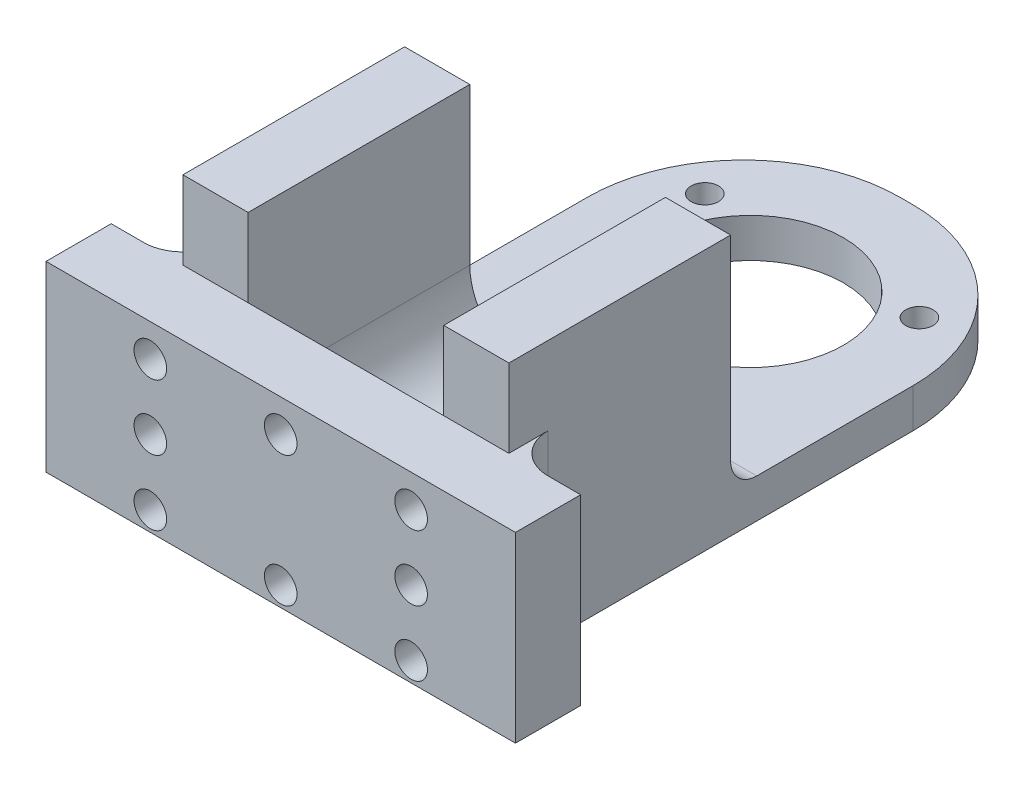
SolidWorks part; units mm, degrees
ref_plane "Front Plane" through (0, 0, 0) normal (0, 0, 1) x (1, 0, 0)
ref_plane "Top Plane" through (0, 0, 0) normal (0, 1, 0) x (1, 0, 0)
ref_plane "Right Plane" through (0, 0, 0) normal (1, 0, 0) x (0, 0, -1)
sketch "Sketch1" plane through (0, 0, 0) normal (0, 0, 1) x (1, 0, 0)
  line L1 (-12.5, -10) -> (12.5, -10)
  line L2 (-12.5, -10) -> (-12.5, 10)
  line L3 (-12.5, 10) -> (12.5, 10)
  line L4 (12.5, -10) -> (12.5, 10)
  line L5 (-12.5, -10) -> (12.5, 10) construction
  line L6 (-12.5, 10) -> (12.5, -10) construction
  point P0 (0, 0)
  point P11 (0, 0)
  point P13 (0, 0.5)
  dimension "D1" = 25
  dimension "D2" = 20
extrude "Main" add sketch "Sketch1" along normal blind 43
sketch "Sketch5" plane through (0, -10, 0) normal (0, -1, 0) x (-1, 0, 0)
  line L0 (0, -21.5) -> (-8.2272, -7.25) construction
  line L1 (-8.2272, -7.25) -> (8.2272, -7.25) construction
  line L2 (8.2272, -7.25) -> (0, -21.5) construction
  line L4 (12.5, 0) -> (-12.5, 0) construction
  circle A0 centre (0, -12) radius 9.5 construction
  circle A1 centre (0, -21.5) radius 1.05
  circle A2 centre (-8.2272, -7.25) radius 1.05
  circle A3 centre (8.2272, -7.25) radius 1.05
  circle A4 centre (0, -12) radius 7.15
  point P11 (0, 0)
  point P12 (0, -12.5)
  point P13 (0, 0)
  point P14 (0, -12.5)
  point P16 (-9.4545, -9.7951)
  point P17 (0, 0)
  point P18 (0, 0)
  dimension "D1" = 19
  dimension "D2" = 2.1
  dimension "D4" = 14.3
  dimension "D3" = 12
extrude "MainAndFixHole" cut sketch "Sketch5" against normal through all
sketch "Sketch6" plane through (0, -10, 0) normal (0, -1, 0) x (-1, 0, 0)
  circle A0 centre (0, -21.5) radius 2.2
  circle A1 centre (-8.2272, -7.25) radius 2.2
  circle A2 centre (8.2272, -7.25) radius 2.2
  dimension "D1" = 4.4
extrude "CoderFixHole2" cut sketch "Sketch6" against normal blind 1.5
sketch "Sketch7" plane through (12.5, 0, 0) normal (1, 0, 0) x (0, 0, -1)
  line L1 (-26, 10) -> (0, 10)
  line L2 (-26, 10) -> (-26, -7)
  line L3 (-26, -7) -> (0, -7)
  line L4 (0, 10) -> (0, -7)
  line L5 (-43, -10) -> (0, -10) construction
  line L7 (0, -10) -> (0, 10) construction
  point P4 (0, 10)
  point P6 (0, 10)
  point P9 (0, -7)
  dimension "D1" = 3
  dimension "D2" = 26
extrude "CoderHole" cut sketch "Sketch7" against normal through all
sketch "Sketch10" plane through (0, 0, 43) normal (0, 0, 1) x (1, 0, 0)
  line L0 (-12.5, -10) -> (12.5, -10) construction
  line L1 (-18, -10) -> (18, -10)
  line L2 (-18, -10) -> (-18, 4)
  line L3 (-18, 4) -> (18, 4)
  line L4 (18, -10) -> (18, 4)
  point P4 (0, -10)
  point P5 (0, -10)
  point P6 (0, 0)
  point P9 (0, -12.7416)
  dimension "D1" = 14
  dimension "D2" = 36
  dimension "D3" = 0
extrude "Link" add sketch "Sketch10" along normal blind 5
sketch "Sketch8" plane through (0, 0, 48) normal (0, 0, 1) x (1, 0, 0)
  line L0 (-10, 1.5) -> (10, 1.5) construction
  line L1 (12.5, 10) -> (-12.5, 10) construction
  line L4 (-18, -10) -> (18, -10) construction
  circle A0 centre (-10, 1.5) radius 1.25
  circle A1 centre (-10, -8.5) radius 1.25
  circle A2 centre (10, -8.5) radius 1.25
  circle A3 centre (10, 1.5) radius 1.25
  circle A4 centre (-10, -3.5) radius 1.25
  circle A5 centre (10, -3.5) radius 1.25
  circle A6 centre (0, 1.5) radius 1.25
  circle A7 centre (0, -8.5) radius 1.25
  point P8 (0, 1.5)
  point P11 (0, 10)
  point P20 (0, 0)
  point P23 (0, 0)
  dimension "D3" = 2.5
  dimension "D5" = 2.5
  dimension "D7" = 2.5
  dimension "D1" = 20
  dimension "D2" = 10
  dimension "D4" = 1.5
  dimension "D6" = 5
extrude "VerticalHoles" cut sketch "Sketch8" against normal blind 10
sketch "Sketch9" plane through (0, 10, 0) normal (0, 1, 0) x (1, 0, 0)
  line L0 (-12.5, -26) -> (12.5, -26) construction
  line L1 (7.5, -26) -> (-7.5, -26)
  line L2 (7.5, -26) -> (7.5, -43)
  line L3 (7.5, -43) -> (-7.5, -43)
  line L4 (-7.5, -26) -> (-7.5, -43)
  line L5 (12.5, -43) -> (-12.5, -43) construction
  line L6 (12.5, -43) -> (12.5, -26) construction
  line L7 (-12.5, -43) -> (-12.5, -26) construction
  dimension "D1" = 5
  dimension "D2" = 5
extrude "Cut-Extrude6" cut sketch "Sketch9" against normal up to surface (17 mm away) up to face at (8.2272, -7, 6.2)
fillet "Fillet2" radius 2 2 edges at (-10, -7, 26) (10, -7, 26)
fillet "Fillet3" radius 5 4 edges at (-7.5, -7, 33.5) (7.5, -7, 33.5) (7.5, -6.4142, 25.4142) (-7.5, -6.4142, 25.4142)
fillet "Fillet4" radius 3 2 edges at (12.5, -3, 43) (-12.5, -3, 43)
fillet "Fillet5" radius 12 2 edges at (-12.5, -8.5, 0) (12.5, -8.5, 0)
